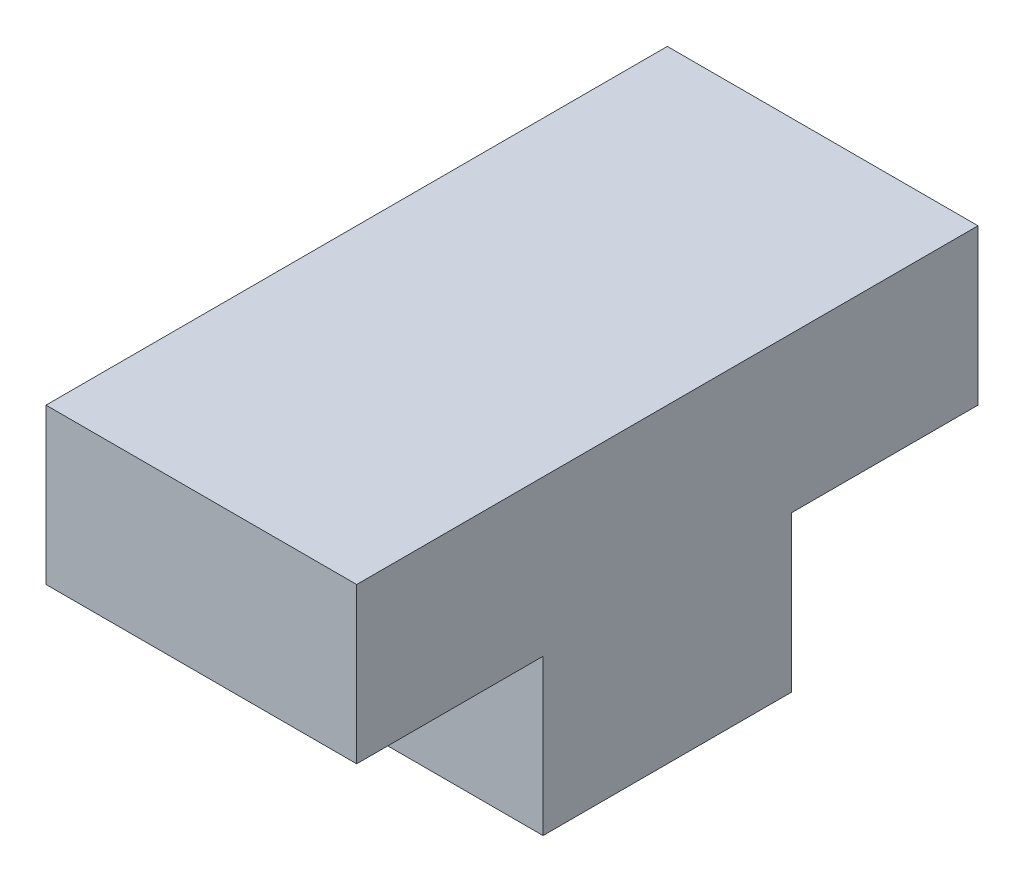
SolidWorks part; units mm, degrees
ref_plane "Front Plane" through (0, 0, 0) normal (0, 0, 1) x (1, 0, 0)
ref_plane "Top Plane" through (0, 0, 0) normal (0, 1, 0) x (1, 0, 0)
ref_plane "Right Plane" through (0, 0, 0) normal (1, 0, 0) x (0, 0, -1)
sketch "Sketch1" plane through (0, 0, 0) normal (1, 0, 0) x (0, 0, -1)
  line L0 (-4, 0) -> (4, 0)
  line L1 (4, 0) -> (4, 5)
  line L2 (4, 5) -> (10, 5)
  line L3 (10, 5) -> (10, 10)
  line L4 (10, 10) -> (-10, 10)
  line L5 (0, 55) -> (0, -55) construction
  line L6 (-10, 5) -> (-10, 10)
  line L7 (-4, 5) -> (-10, 5)
  line L8 (-4, 0) -> (-4, 5)
  point P11 (0, 10)
  point P14 (0, 0)
  dimension "D1" = 4
  dimension "D2" = 5
  dimension "D3" = 5
  dimension "D4" = 10
extrude "Boss-Extrude1" add sketch "Sketch1" along normal blind 10
